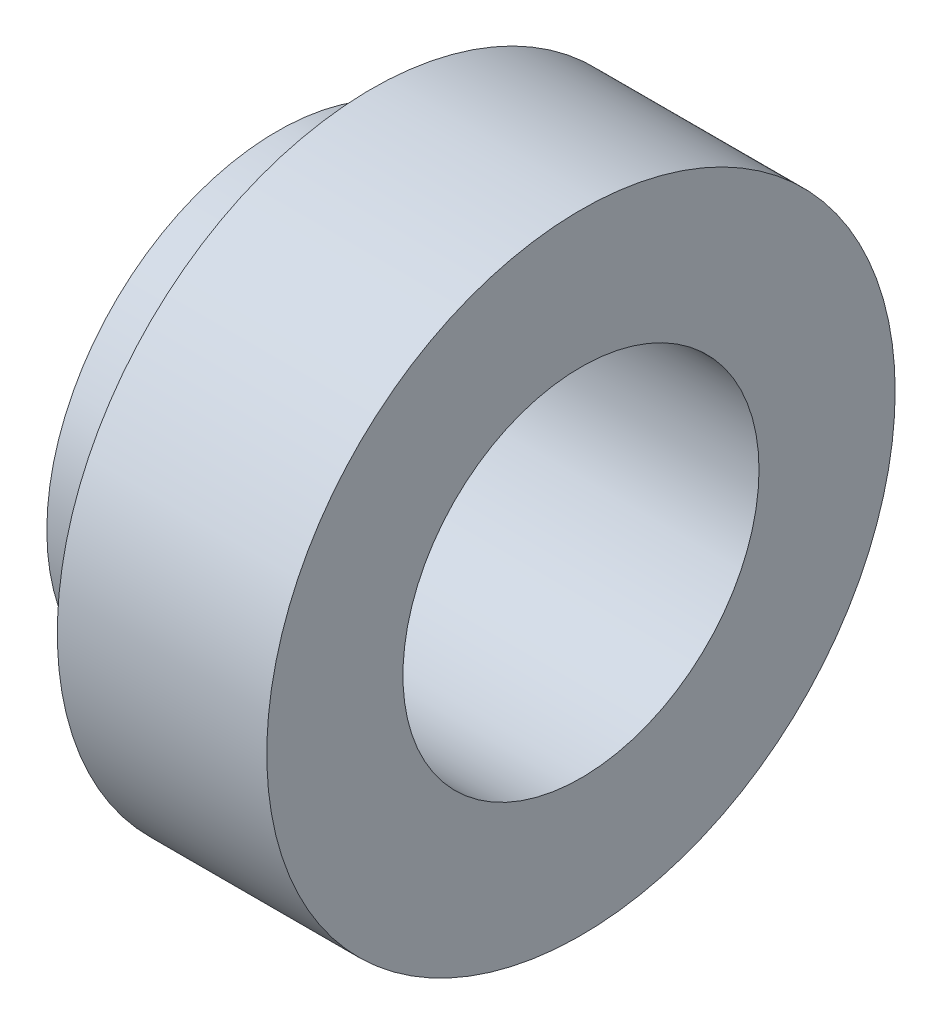
SolidWorks part; units mm, degrees
material "1.0037 (S235JR)"
ref_plane "Front Plane" through (0, 0, 0) normal (0, 0, 1) x (1, 0, 0)
ref_plane "Top Plane" through (0, 0, 0) normal (0, 1, 0) x (1, 0, 0)
ref_plane "Right Plane" through (0, 0, 0) normal (1, 0, 0) x (0, 0, -1)
sketch "Sketch1" plane through (0, 0, 0) normal (0, 0, 1) x (1, 0, 0)
  line L0 (0, 0) -> (0, 11)
  line L1 (0, 11) -> (4.5, 11)
  line L2 (4.5, 11) -> (4.5, 15)
  line L3 (4.5, 15) -> (14.5, 15)
  line L4 (14.5, 15) -> (14.5, 0)
  line L5 (14.5, 0) -> (0, 0) construction
  line L6 (0, 8.5) -> (14.5, 8.5)
  dimension "D1" = 4.5
  dimension "D2" = 10
  dimension "D3" = 22
  dimension "D4" = 17
  dimension "D5" = 30
revolve "Revolve1" add sketch "Sketch1" angle 360 about L5
